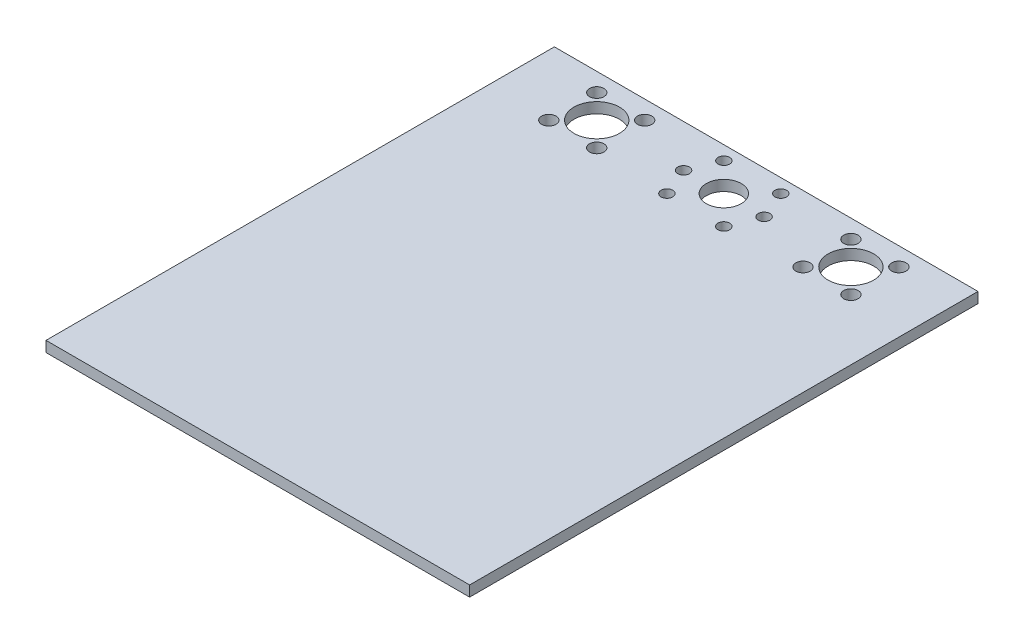
SolidWorks part; units mm, degrees
ref_plane "Front Plane" through (0, 0, 0) normal (0, 0, 1) x (1, 0, 0)
ref_plane "Top Plane" through (0, 0, 0) normal (0, 1, 0) x (1, 0, 0)
ref_plane "Right Plane" through (0, 0, 0) normal (1, 0, 0) x (0, 0, -1)
sketch "Sketch1" plane through (0, 0, 0) normal (0, 1, 0) x (1, 0, 0)
  line L1 (-100, -120) -> (100, -120)
  line L2 (-100, -120) -> (-100, 120)
  line L3 (-100, 120) -> (100, 120)
  line L4 (100, -120) -> (100, 120)
  line L5 (-100, -120) -> (100, 120) construction
  line L6 (-100, 120) -> (100, -120) construction
  point P0 (0, 0)
  dimension "D1" = 200
  dimension "D2" = 240
extrude "Boss-Extrude1" add sketch "Sketch1" along normal blind 5
sketch "Sketch3" plane through (0, 5, 0) normal (0, 1, 0) x (1, 0, 0)
  line L0 (100, 120) -> (-100, 120) construction
  circle A0 centre (0, 100) radius 8.25
  point P2 (0, 0)
  point P5 (0, 120)
  point P6 (0, 0)
  dimension "D1" = 16.5
  dimension "D2" = 20
extrude "Cut-Extrude1" cut sketch "Sketch3" against normal through all
sketch "Sketch4" plane through (0, 5, 0) normal (0, 1, 0) x (1, 0, 0)
  line L0 (0, 100) -> (19, 100) construction
  line L1 (0, 100) -> (13.435, 113.435) construction
  line L2 (0, 100) -> (19, 100) construction
  line L3 (0, 100) -> (13.435, 86.565) construction
  line L4 (0, -2.75) -> (0, 2.75) construction
  circle A0 centre (0, 100) radius 19 construction
  circle A1 centre (19, 100) radius 2.75
  circle A2 centre (13.435, 113.435) radius 2.75
  circle A3 centre (13.435, 86.565) radius 2.75
  circle A4 centre (-13.435, 86.565) radius 2.75
  circle A5 centre (-19, 100) radius 2.75
  circle A6 centre (-13.435, 113.435) radius 2.75
  point P6 (0, 0)
  dimension "D1" = 38
  dimension "D2" = 5.5
  dimension "D4" = 45
  dimension "D5" = 19
  dimension "D7" = 45
  dimension "D8" = 19
  dimension "D3" = 2
  dimension "D6" = 2
extrude "Cut-Extrude2" cut sketch "Sketch4" against normal through all
sketch "Sketch5" plane through (0, 5, 0) normal (0, 1, 0) x (1, 0, 0)
  line L0 (100, 120) -> (-100, 120) construction
  line L1 (-100, 120) -> (-100, -120) construction
  line L2 (0, -2.75) -> (0, 2.75) construction
  circle A0 centre (-60, 100) radius 10.75
  circle A1 centre (60, 100) radius 10.75
  point P2 (0, 0)
  point P5 (-60.2581, 100)
  dimension "D1" = 21.5
  dimension "D2" = 20
  dimension "D3" = 40
extrude "Cut-Extrude4" cut sketch "Sketch5" against normal through all contours A0 | A1
sketch "Sketch6" plane through (0, 5, 0) normal (0, 1, 0) x (1, 0, 0)
  line L0 (-60, 100) -> (-48.6863, 111.3137) construction
  line L1 (-60, 100) -> (-34.215, 100) construction
  circle A0 centre (-60, 100) radius 16 construction
  circle A1 centre (-48.6863, 111.3137) radius 3.4
  circle A2 centre (-48.6863, 88.6863) radius 3.4
  circle A3 centre (-71.3137, 88.6863) radius 3.4
  circle A4 centre (-71.3137, 111.3137) radius 3.4
  point P3 (-70.2393, 110.1259)
  point P5 (0, 0)
  point P7 (0, 0)
  point P16 (-68.0251, 106.54)
  point P17 (0, 0)
  dimension "D1" = 32
  dimension "D2" = 6.8
  dimension "D4" = 16
  dimension "D5" = 45
  dimension "D3" = 4
extrude "Cut-Extrude5" cut sketch "Sketch6" against normal through all
mirror "Mirror1" about plane through (0, 0, 0) normal (1, 0, 0) of "Cut-Extrude5"
